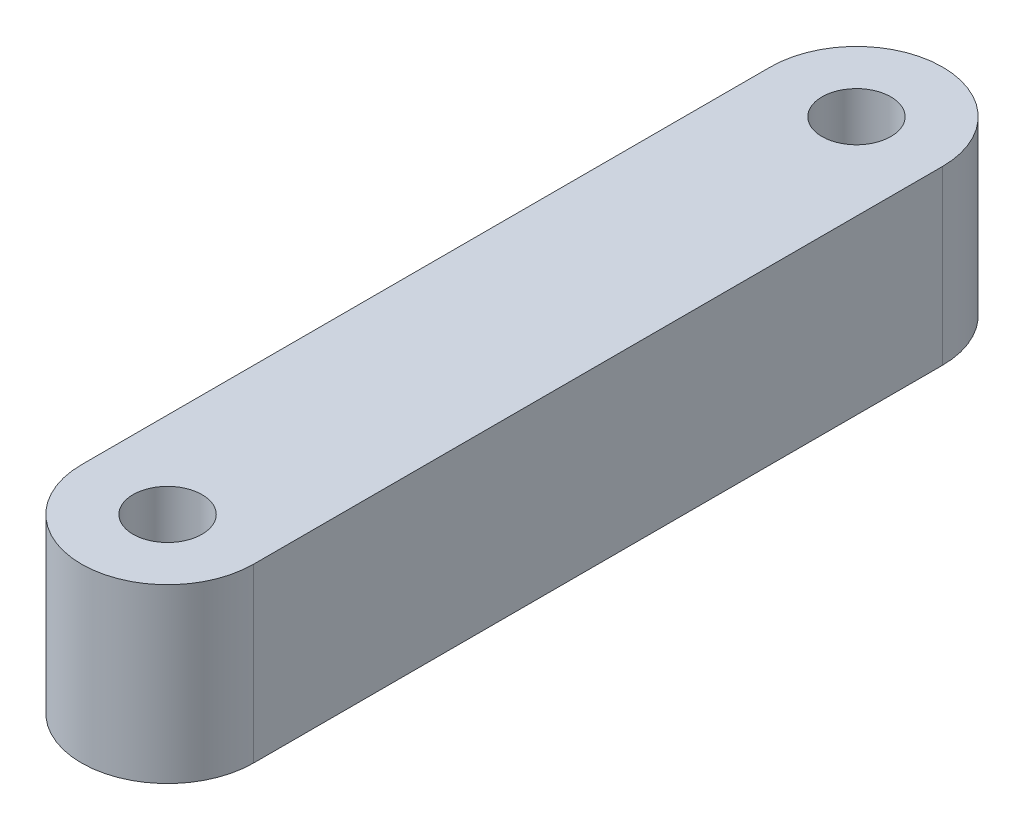
SolidWorks part; units mm, degrees
ref_plane "Front Plane" through (0, 0, 0) normal (0, 0, 1) x (1, 0, 0)
ref_plane "Top Plane" through (0, 0, 0) normal (0, 1, 0) x (1, 0, 0)
ref_plane "Right Plane" through (0, 0, 0) normal (1, 0, 0) x (0, 0, -1)
sketch "Sketch1" plane through (0, 0, 0) normal (0, 1, 0) x (1, 0, 0)
  line L0 (-5, 40) -> (-5, 0)
  line L2 (5, 0) -> (5, 40)
  arc A0 (-5, 0) -> (5, 0) centre (0, 0) ccw
  arc A1 (5, 40) -> (-5, 40) centre (0, 40) ccw
  circle A2 centre (0, 40) radius 2
  circle A3 centre (0, 0) radius 2
  point P11 (0, 71.4578)
  dimension "D1" = 4
  dimension "D2" = 10
  dimension "D3" = 40
extrude "Boss-Extrude1" add sketch "Sketch1" along normal blind 10 contours L2 A1 L0 A0 A3 A2
